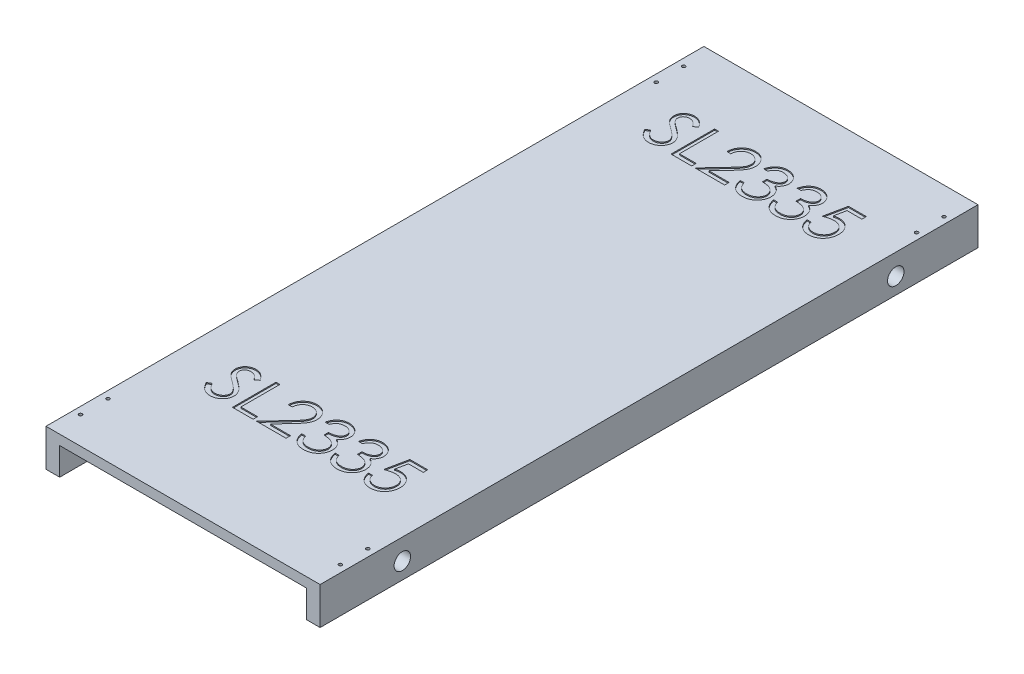
SolidWorks part; units mm, degrees
ref_plane "Front Plane" through (0, 0, 0) normal (0, 0, 1) x (1, 0, 0)
ref_plane "Top Plane" through (0, 0, 0) normal (0, 1, 0) x (1, 0, 0)
ref_plane "Right Plane" through (0, 0, 0) normal (1, 0, 0) x (0, 0, -1)
sketch "Sketch1" plane through (0, 0, 0) normal (0, 0, 1) x (1, 0, 0)
  line L1 (0, 0) -> (25, 0)
  line L2 (0, 0) -> (0, 68)
  line L4 (25, 0) -> (25, 50)
  line L5 (0, 68) -> (500, 68)
  line L7 (25, 50) -> (475, 50)
  line L10 (500, 68) -> (500, 0)
  line L11 (500, 0) -> (475, 0)
  line L12 (475, 50) -> (475, 0)
  dimension "D1" = 25
  dimension "D2" = 68
  dimension "D3" = 50
  dimension "D5" = 25
  dimension "D6" = 68
extrude "Boss-Extrude1" add sketch "Sketch1" along normal blind 1200
sketch "Sketch2" plane through (500, 0, 0) normal (1, 0, 0) x (0, 0, -1)
  line L0 (-1200, 0) -> (0, 0) construction
  line L1 (-1200, 0) -> (-1200, 68) construction
  circle A0 centre (-1050, 30) radius 15
  dimension "D1" = 30
  dimension "D2" = 30
  dimension "D3" = 150
extrude "Cut-Extrude1" cut sketch "Sketch2" against normal blind 1200
sketch "Sketch4" plane through (500, 0, 0) normal (1, 0, 0) x (0, 0, -1)
  line L0 (-1200, 0) -> (0, 0) construction
  line L1 (0, 0) -> (0, 68) construction
  circle A0 centre (-150, 30) radius 15
  dimension "D1" = 30
  dimension "D2" = 30
  dimension "D3" = 150
extrude "Cut-Extrude2" cut sketch "Sketch4" against normal blind 1200
sketch "Sketch9" plane through (0, 68, 0) normal (0, 1, 0) x (1, 0, 0)
  line L2 (0, -1200) -> (0, 0) construction
  line L3 (500, 0) -> (0, 0) construction
  text T0 "SL2335" font "Century Gothic" height in points 300
  dimension "D1" = 75
  dimension "D2" = 200
extrude "Cut-Extrude3" cut sketch "Sketch9" against normal blind 2
sketch "Sketch11" plane through (0, 68, 0) normal (0, 1, 0) x (1, 0, 0)
  line L0 (0, -1200) -> (0, 0) construction
  line L1 (500, -1200) -> (0, -1200) construction
  text T0 "SL2335" font "Century Gothic" height in points 300
  dimension "D1" = 75
  dimension "D2" = 200
extrude "Cut-Extrude6" cut sketch "Sketch11" against normal blind 2
sketch "Sketch14" plane through (0, 0, 0) normal (0, -1, 0) x (-1, 0, 0)
  line L0 (-475, 0) -> (-500, 0) construction
  line L1 (-475, -1200) -> (-475, 0) construction
  line L2 (0, 0) -> (-25, 0) construction
  line L3 (0, -1200) -> (0, 0) construction
  line L4 (0, -1200) -> (-25, -1200) construction
  line L5 (-475, -1200) -> (-500, -1200) construction
  line L6 (-500, -1200) -> (-500, 0) construction
  point P0 (-13, -50)
  point P2 (-13, -100)
  point P4 (-13, -1100)
  point P6 (-13, -1150)
  point P8 (-487, -1100)
  point P10 (-487, -1150)
  point P12 (-488, -50)
  point P14 (-488, -100)
  point P21 (0, 0)
  dimension "D1" = 50
  dimension "D2" = 100
  dimension "D3" = 13
  dimension "D4" = 13
  dimension "D5" = 50
  dimension "D6" = 100
  dimension "D7" = 13
  dimension "D8" = 13
  dimension "D9" = 100
  dimension "D10" = 50
  dimension "D11" = 13
  dimension "D12" = 13
  dimension "D13" = 50
  dimension "D14" = 100
  dimension "D15" = 13
  dimension "D16" = 13
hole_wizard "Ø6.0 (6) Diameter Hole1" positions "Sketch14" profile "Sketch13" hole size "Ø6.0" standard "ISO" end condition through all
sketch "Sketch13" plane through (13, 0, 50) normal (1, 0, 0) x (0, 0, -1)
  line L0 (0, 0) -> (0, 68)
  line L1 (0, 68) -> (3, 68)
  line L2 (3, 68) -> (3, 0.025)
  line L3 (3, 0.025) -> (3.025, 0)
  line L5 (3.025, 0) -> (0, 0)
  line L6 (-3, 0.025) -> (-3.025, 0) construction
  line L11 (0, -6.35) -> (0, 107.95) construction
  dimension "Thru Hole Dia." = 6
  dimension "Thru Hole Depth" = 68
  dimension "Near C'Sink Dia." = 6.05
  dimension "Near C'Sink Angle" = 90
